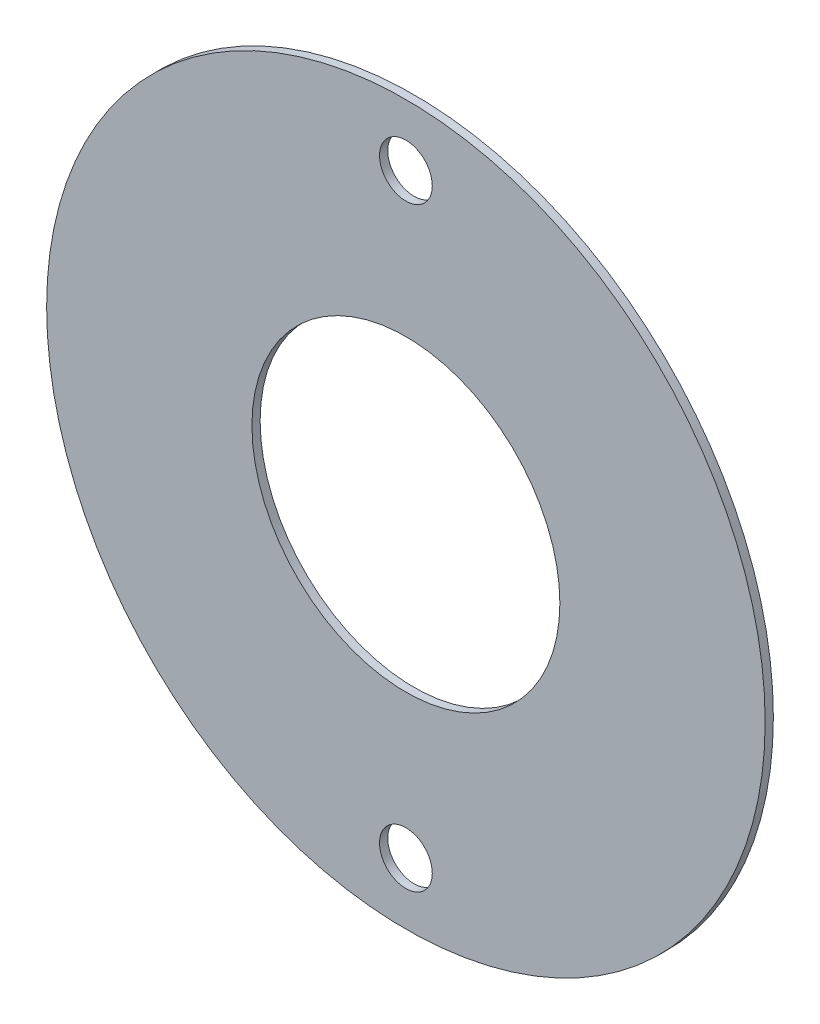
SolidWorks part; units mm, degrees
ref_plane "Front Plane" through (0, 0, 0) normal (0, 0, 1) x (1, 0, 0)
ref_plane "Top Plane" through (0, 0, 0) normal (0, 1, 0) x (1, 0, 0)
ref_plane "Right Plane" through (0, 0, 0) normal (1, 0, 0) x (0, 0, -1)
sketch "Sketch1" plane through (0, 0, 0) normal (0, 0, 1) x (1, 0, 0)
  circle A0 centre (0, 0) radius 22.225
  dimension "D1" = 44.45
extrude "Boss-Extrude1" add sketch "Sketch1" along normal blind 0.508
sketch "Sketch2" plane through (0, 0, 0.508) normal (0, 0, 1) x (1, 0, 0)
  circle A0 centre (0, 0) radius 9.525
  dimension "D1" = 19.05
extrude "Cut-Extrude1" cut sketch "Sketch2" against normal through all
hole_wizard "#30 (0.1285) Diameter Hole1" positions "Sketch4" profile "Sketch5" hole size "#30" standard "ANSI Inch" end condition through all
sketch "Sketch4" plane through (0, 0, 0.508) normal (0, 0, 1) x (1, 0, 0)
  point P0 (0, 18.415)
  dimension "D1" = 18.415
sketch "Sketch5" plane through (0, 18.415, 0.508) normal (1, 0, 0) x (0, -1, 0)
  line L0 (0, 0) -> (0, 0.508)
  line L1 (0, 0.508) -> (1.6319, 0.508)
  line L2 (1.6319, 0.508) -> (1.6319, 0)
  line L5 (1.6319, 0) -> (0, 0)
  line L11 (0, -6.35) -> (0, 107.95) construction
  dimension "Thru Hole Dia." = 3.2639
  dimension "Thru Hole Depth" = 0.508
mirror "Mirror1" about plane through (0, 0, 0) normal (0, 1, 0) of "#30 (0.1285) Diameter Hole1"
